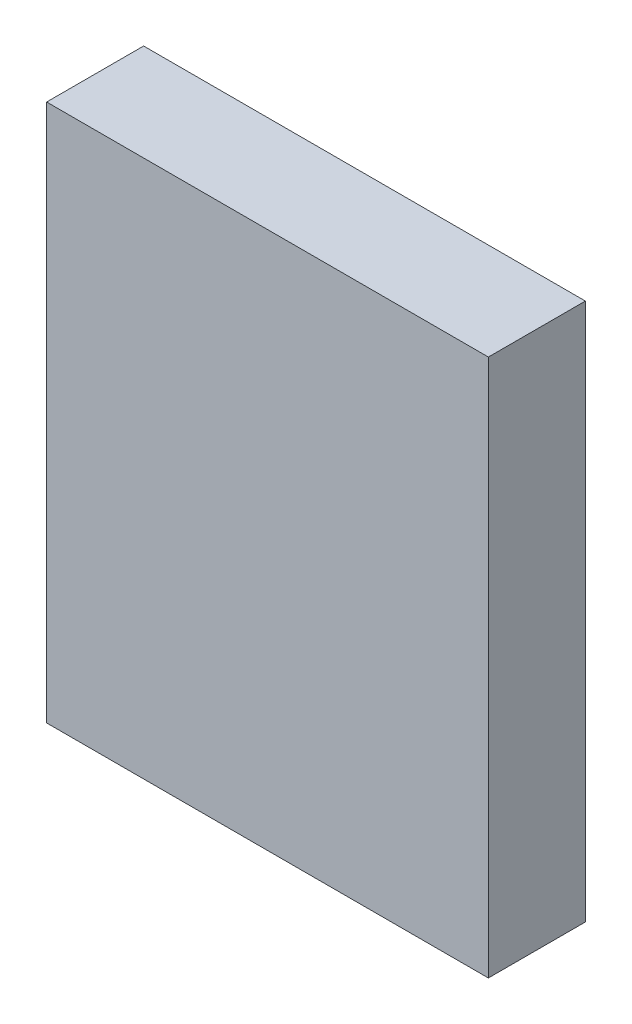
SolidWorks part; units mm, degrees
ref_plane "Piano frontale" through (0, 0, 0) normal (0, 0, 1) x (1, 0, 0)
ref_plane "Piano superiore" through (0, 0, 0) normal (0, 1, 0) x (1, 0, 0)
ref_plane "Piano destro" through (0, 0, 0) normal (1, 0, 0) x (0, 0, -1)
sketch "Schizzo1" plane through (0, 0, 0) normal (0, 0, 1) x (1, 0, 0)
  line L1 (0, 0) -> (46, 0)
  line L2 (0, 0) -> (0, 56)
  line L3 (0, 56) -> (46, 56)
  line L4 (46, 0) -> (46, 56)
  dimension "D1" = 56
  dimension "D2" = 46
extrude "Estrusione-Estrusione1" add sketch "Schizzo1" along normal blind 10.1
